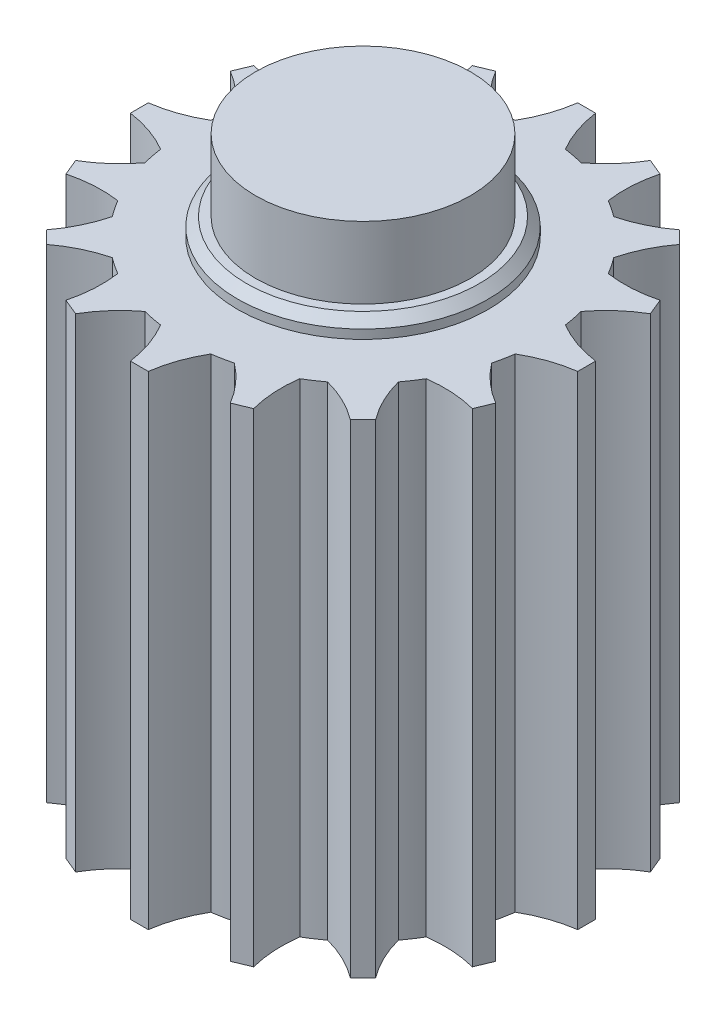
SolidWorks part; units mm, degrees
ref_plane "Front Plane" through (0, 0, 0) normal (0, 0, 1) x (1, 0, 0)
ref_plane "Top Plane" through (0, 0, 0) normal (0, 1, 0) x (1, 0, 0)
ref_plane "Right Plane" through (0, 0, 0) normal (1, 0, 0) x (0, 0, -1)
sketch "Sketch1" plane through (0, 0, 0) normal (0, 1, 0) x (1, 0, 0)
  line L0 (0, 0) -> (0, 16.7331) construction
  line L1 (-0.5, 12.49) -> (0.5, 12.49)
  line L2 (4.3178, 11.7306) -> (5.2417, 11.3479)
  line L3 (8.4782, 9.1853) -> (9.1853, 8.4782)
  line L4 (11.3479, 5.2417) -> (11.7306, 4.3178)
  line L5 (12.49, 0.5) -> (12.49, -0.5)
  line L6 (11.7306, -4.3178) -> (11.3479, -5.2417)
  line L7 (9.1853, -8.4782) -> (8.4782, -9.1853)
  line L8 (5.2417, -11.3479) -> (4.3178, -11.7306)
  line L9 (0.5, -12.49) -> (-0.5, -12.49)
  line L10 (-4.3178, -11.7306) -> (-5.2417, -11.3479)
  line L11 (-8.4782, -9.1853) -> (-9.1853, -8.4782)
  line L12 (-11.3479, -5.2417) -> (-11.7306, -4.3178)
  line L13 (-12.49, -0.5) -> (-12.49, 0.5)
  line L14 (-11.7306, 4.3178) -> (-11.3479, 5.2417)
  line L15 (-9.1853, 8.4782) -> (-8.4782, 9.1853)
  line L16 (-5.2417, 11.3479) -> (-4.3178, 11.7306)
  circle A0 centre (0, 0) radius 10
  arc A2 (-1.4, 9.9015) -> (-0.5, 12.49) centre (-7.4338, 13.4501) ccw
  arc A3 (1.4, 9.9015) -> (0.5, 12.49) centre (7.4338, 13.4501) cw
  arc A4 (2.4957, 9.6836) -> (4.3178, 11.7306) centre (-1.7208, 15.2711) ccw
  arc A5 (5.0826, 8.6121) -> (5.2417, 11.3479) centre (12.0151, 9.5815) cw
  arc A6 (6.0115, 7.9914) -> (8.4782, 9.1853) centre (4.2542, 14.7672) ccw
  arc A7 (7.9914, 6.0115) -> (9.1853, 8.4782) centre (14.7672, 4.2542) cw
  arc A8 (8.6121, 5.0826) -> (11.3479, 5.2417) centre (9.5815, 12.0151) ccw
  arc A9 (9.6836, 2.4957) -> (11.7306, 4.3178) centre (15.2711, -1.7208) cw
  arc A10 (9.9015, 1.4) -> (12.49, 0.5) centre (13.4501, 7.4338) ccw
  arc A11 (9.9015, -1.4) -> (12.49, -0.5) centre (13.4501, -7.4338) cw
  arc A12 (9.6836, -2.4957) -> (11.7306, -4.3178) centre (15.2711, 1.7208) ccw
  arc A13 (8.6121, -5.0826) -> (11.3479, -5.2417) centre (9.5815, -12.0151) cw
  arc A14 (7.9914, -6.0115) -> (9.1853, -8.4782) centre (14.7672, -4.2542) ccw
  arc A15 (6.0115, -7.9914) -> (8.4782, -9.1853) centre (4.2542, -14.7672) cw
  arc A16 (5.0826, -8.6121) -> (5.2417, -11.3479) centre (12.0151, -9.5815) ccw
  arc A17 (2.4957, -9.6836) -> (4.3178, -11.7306) centre (-1.7208, -15.2711) cw
  arc A18 (1.4, -9.9015) -> (0.5, -12.49) centre (7.4338, -13.4501) ccw
  arc A19 (-1.4, -9.9015) -> (-0.5, -12.49) centre (-7.4338, -13.4501) cw
  arc A20 (-2.4957, -9.6836) -> (-4.3178, -11.7306) centre (1.7208, -15.2711) ccw
  arc A21 (-5.0826, -8.6121) -> (-5.2417, -11.3479) centre (-12.0151, -9.5815) cw
  arc A22 (-6.0115, -7.9914) -> (-8.4782, -9.1853) centre (-4.2542, -14.7672) ccw
  arc A23 (-7.9914, -6.0115) -> (-9.1853, -8.4782) centre (-14.7672, -4.2542) cw
  arc A24 (-8.6121, -5.0826) -> (-11.3479, -5.2417) centre (-9.5815, -12.0151) ccw
  arc A25 (-9.6836, -2.4957) -> (-11.7306, -4.3178) centre (-15.2711, 1.7208) cw
  arc A26 (-9.9015, -1.4) -> (-12.49, -0.5) centre (-13.4501, -7.4338) ccw
  arc A27 (-9.9015, 1.4) -> (-12.49, 0.5) centre (-13.4501, 7.4338) cw
  arc A28 (-9.6836, 2.4957) -> (-11.7306, 4.3178) centre (-15.2711, -1.7208) ccw
  arc A29 (-8.6121, 5.0826) -> (-11.3479, 5.2417) centre (-9.5815, 12.0151) cw
  arc A30 (-7.9914, 6.0115) -> (-9.1853, 8.4782) centre (-14.7672, 4.2542) ccw
  arc A31 (-6.0115, 7.9914) -> (-8.4782, 9.1853) centre (-4.2542, 14.7672) cw
  arc A32 (-5.0826, 8.6121) -> (-5.2417, 11.3479) centre (-12.0151, 9.5815) ccw
  arc A33 (-2.4957, 9.6836) -> (-4.3178, 11.7306) centre (1.7208, 15.2711) cw
  point P104 (0, 0)
  dimension "D1" = 20
  dimension "D5" = 7
  dimension "D3" = 0.5
  dimension "D4" = 1.4
  dimension "D6" = 16
extrude "Boss-Extrude1" add sketch "Sketch1" along normal blind 27
sketch "Sketch2" plane through (0, 27, 0) normal (0, 1, 0) x (1, 0, 0)
  circle A0 centre (0, 0) radius 6
  dimension "D1" = 12
extrude "Boss-Extrude2" add sketch "Sketch2" along normal blind 4
sketch "Sketch4" plane through (0, 27, 0) normal (0, 1, 0) x (1, 0, 0)
  circle A0 centre (0, 0) radius 7
  dimension "D1" = 14
extrude "Boss-Extrude3" add sketch "Sketch4" along normal blind 1
sketch "Sketch5" plane through (0, 31, 0) normal (0, 1, 0) x (1, 0, 0)
  circle A0 centre (0, 0) radius 6
  dimension "D1" = 12
extrude "Boss-Extrude4" add sketch "Sketch5" along normal blind 1
chamfer "Chamfer1" distance 0.5 angle 45 1 edges at (0, 28, 7)
